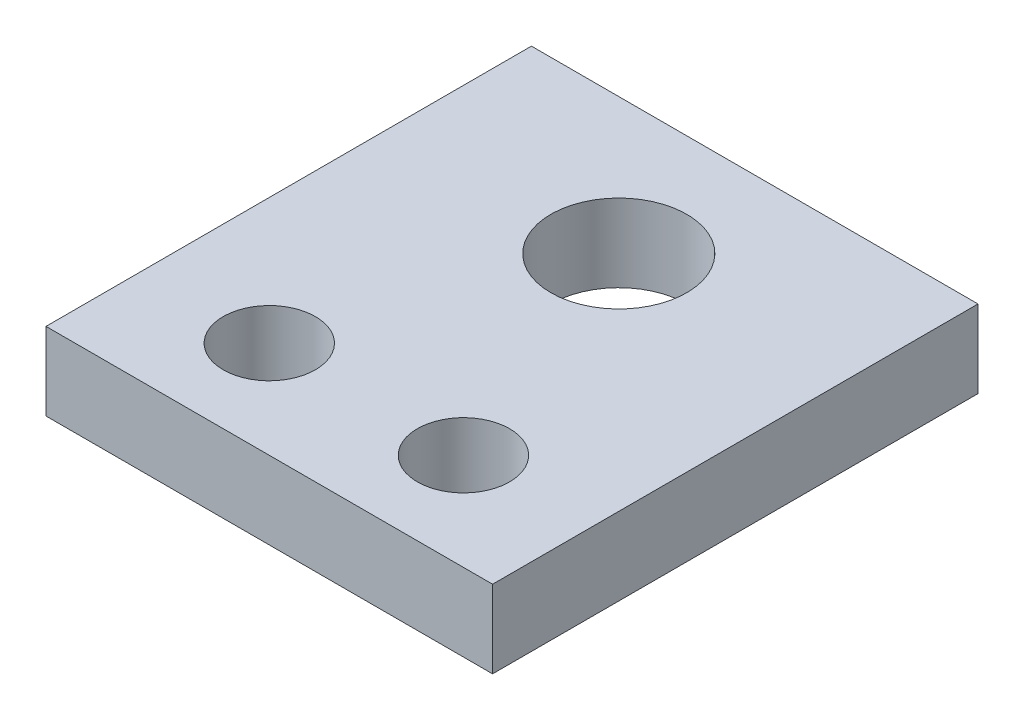
SolidWorks part; units mm, degrees
ref_plane "前视基准面" through (0, 0, 0) normal (0, 0, 1) x (1, 0, 0)
ref_plane "上视基准面" through (0, 0, 0) normal (0, 1, 0) x (1, 0, 0)
ref_plane "右视基准面" through (0, 0, 0) normal (1, 0, 0) x (0, 0, -1)
sketch "草图1" plane through (0, 0, 0) normal (0, 1, 0) x (1, 0, 0)
  line L1 (-23, 25) -> (23, 25)
  line L2 (-23, 25) -> (-23, -25)
  line L3 (-23, -25) -> (23, -25)
  line L4 (23, 25) -> (23, -25)
  line L5 (-23, 25) -> (23, -25) construction
  line L6 (-23, -25) -> (23, 25) construction
  point P0 (0, 0)
  dimension "D1" = 46
  dimension "D2" = 50
extrude "凸台-拉伸1" add sketch "草图1" along normal blind 8
sketch "草图2" plane through (0, 8, 0) normal (0, 1, 0) x (1, 0, 0)
  line L0 (0, 0) -> (0, -26.0305) construction
  line L2 (-23, -25) -> (23, -25) construction
  circle A0 centre (0, 11) radius 7
  circle A1 centre (-10, -15) radius 4.75
  circle A2 centre (10, -15) radius 4.75
  dimension "D1" = 14
  dimension "D2" = 9.5
  dimension "D3" = 36
  dimension "D4" = 10
  dimension "D5" = 20
extrude "切除-拉伸1" cut sketch "草图2" against normal blind 8
